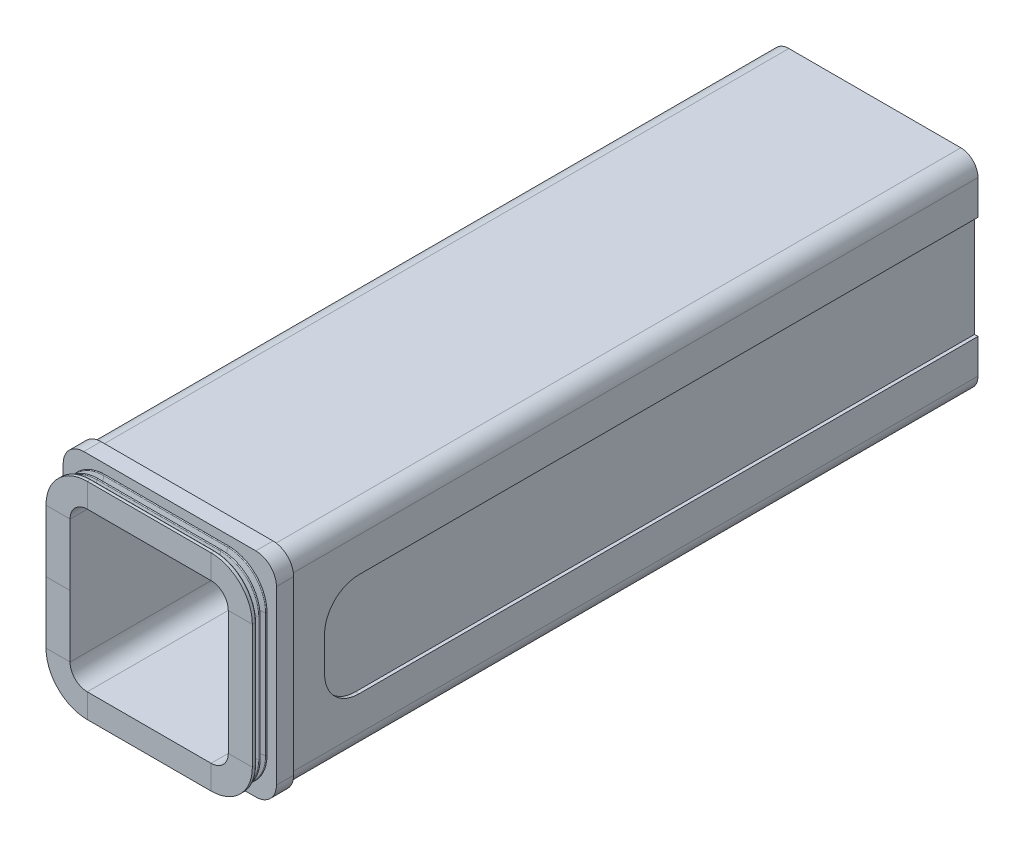
SolidWorks part; units mm, degrees
ref_plane "Front Plane" through (0, 0, 0) normal (0, 0, 1) x (1, 0, 0)
ref_plane "Top Plane" through (0, 0, 0) normal (0, 1, 0) x (1, 0, 0)
ref_plane "Right Plane" through (0, 0, 0) normal (1, 0, 0) x (0, 0, -1)
sketch "Sketch1" plane through (0, 0, 0) normal (0, 0, 1) x (1, 0, 0)
  line L1 (-25, -30) -> (25, -30)
  line L2 (-30, -25) -> (-30, 25)
  line L3 (-25, 30) -> (25, 30)
  line L4 (30, -25) -> (30, 25)
  line L5 (-30, -30) -> (30, 30) construction
  line L6 (-30, 30) -> (30, -30) construction
  arc A0 (-25, -30) -> (-30, -25) centre (-25, -25) cw
  arc A1 (25, -30) -> (30, -25) centre (25, -25) ccw
  arc A2 (25, 30) -> (30, 25) centre (25, 25) cw
  arc A3 (-30, 25) -> (-25, 30) centre (-25, 25) cw
  point P0 (0, 0)
  dimension "D3" = 5
  dimension "D1" = 60
  dimension "D2" = 60
extrude "Boss-Extrude1" add sketch "Sketch1" along normal blind 200
sketch "Sketch2" plane through (0, 0, 200) normal (0, 0, 1) x (1, 0, 0)
  line L8 (-25, -31) -> (25, -31)
  line L9 (31, -25) -> (31, 25)
  line L10 (25, 31) -> (-25, 31)
  line L11 (-31, 25) -> (-31, -25)
  line L12 (-25, -31) -> (25, -31)
  line L13 (31, -25) -> (31, 25)
  line L14 (25, 31) -> (-25, 31)
  line L15 (-31, 25) -> (-31, -25)
  arc A8 (-31, -25) -> (-25, -31) centre (-25, -25) ccw
  arc A9 (25, -31) -> (31, -25) centre (25, -25) ccw
  arc A10 (31, 25) -> (25, 31) centre (25, 25) ccw
  arc A11 (-25, 31) -> (-31, 25) centre (-25, 25) ccw
  arc A12 (-31, -25) -> (-25, -31) centre (-25, -25) ccw
  arc A13 (25, -31) -> (31, -25) centre (25, -25) ccw
  arc A14 (31, 25) -> (25, 31) centre (25, 25) ccw
  arc A15 (-25, 31) -> (-31, 25) centre (-25, 25) ccw
  dimension "D1" = 1
extrude "Boss-Extrude2" add sketch "Sketch2" along normal blind 5
ref_plane "Plane1" through (0, 0, 0) normal (0, 1, 0) x (1, 0, 0)
sketch "Sketch3" plane through (0, 0, 0) normal (0, 1, 0) x (1, 0, 0)
  line L0 (25, -205) -> (-25, -205) construction
  line L1 (25, -205) -> (-25, -205) construction
  line L2 (-25, -205) -> (-29.0194, -205.8039)
  line L3 (-29.0194, -206.1961) -> (-25.9806, -206.8039)
  line L4 (-25.9806, -207.1961) -> (-29.0194, -207.8039)
  line L5 (-29.0194, -208.1961) -> (-25.9806, -208.8039)
  line L6 (-25.9806, -209.1961) -> (-29.8392, -209.9678)
  line L7 (-30, -210.164) -> (-30, -211)
  line L8 (-30, -211) -> (-23, -211)
  line L9 (-23, -211) -> (-23, -205)
  line L10 (-23, -205) -> (-25, -205)
  line L11 (-30, -210) -> (-30, -208) construction
  line L12 (-30, -206) -> (-30, -208) construction
  line L13 (-30, -206) -> (-30, -205) construction
  line L14 (-30, -205) -> (-25, -205) construction
  arc A0 (-29.8392, -209.9678) -> (-30, -210.164) centre (-29.8, -210.164) ccw
  arc A1 (-29.0194, -205.8039) -> (-29.0194, -206.1961) centre (-28.9802, -206) ccw
  arc A2 (-29.0194, -207.8039) -> (-29.0194, -208.1961) centre (-28.9802, -208) ccw
  arc A3 (-25.9806, -208.8039) -> (-25.9806, -209.1961) centre (-26.0198, -209) cw
  arc A4 (-25.9806, -206.8039) -> (-25.9806, -207.1961) centre (-26.0198, -207) cw
  point P2 (0, 0)
  point P25 (-25, -207)
  dimension "D7" = 0.2
  dimension "D1" = 1
  dimension "D2" = 2
  dimension "D3" = 1
  dimension "D4" = 5
  dimension "D5" = 2
  dimension "D6" = 2
sketch "Sketch5" plane through (0, 0, 205) normal (0, 0, 1) x (1, 0, 0)
  line L1 (18, -23) -> (-18, -23)
  line L2 (23, -18) -> (23, 18)
  line L3 (18, 23) -> (-18, 23)
  line L4 (-23, -18) -> (-23, 18)
  line L5 (23, -23) -> (-23, 23) construction
  line L6 (23, 23) -> (-23, -23) construction
  arc A0 (-18, -23) -> (-23, -18) centre (-18, -18) cw
  arc A1 (18, -23) -> (23, -18) centre (18, -18) ccw
  arc A2 (23, 18) -> (18, 23) centre (18, 18) ccw
  arc A3 (-18, 23) -> (-23, 18) centre (-18, 18) ccw
  point P0 (0, 0)
  dimension "D1" = 5
sweep "Sweep1" add profiles "Sketch3" path "Sketch5"
sketch "Sketch6" plane through (0, 0, 205) normal (0, 0, 1) x (1, 0, 0)
  line L5 (-23, 18) -> (-23, 0)
  line L6 (-23, 0) -> (-23, -18)
  line L7 (-18, -23) -> (18, -23)
  line L8 (23, -18) -> (23, 18)
  line L9 (18, 23) -> (-18, 23)
  line L10 (-23, 18) -> (-23, 0)
  line L11 (-23, 0) -> (-23, -18)
  line L12 (-18, -23) -> (18, -23)
  line L13 (23, -18) -> (23, 18)
  line L14 (18, 23) -> (-18, 23)
  arc A4 (-23, -18) -> (-18, -23) centre (-18, -18) ccw
  arc A5 (18, -23) -> (23, -18) centre (18, -18) ccw
  arc A6 (23, 18) -> (18, 23) centre (18, 18) ccw
  arc A7 (-18, 23) -> (-23, 18) centre (-18, 18) ccw
  arc A8 (-23, -18) -> (-18, -23) centre (-18, -18) ccw
  arc A9 (18, -23) -> (23, -18) centre (18, -18) ccw
  arc A10 (23, 18) -> (18, 23) centre (18, 18) ccw
  arc A11 (-18, 23) -> (-23, 18) centre (-18, 18) ccw
  dimension "D1" = 0
extrude "Cut-Extrude1" cut sketch "Sketch6" against normal through all
sketch "Sketch7" plane through (-30, 0, 0) normal (-1, 0, 0) x (0, 0, 1)
  line L6 (0, 15) -> (0, -15)
  line L9 (0, -15) -> (190, -15)
  line L10 (190, -15) -> (190, 15)
  line L11 (190, 15) -> (0, 15)
  line L12 (0, -15) -> (190, -15)
  line L13 (190, -15) -> (190, 15)
  line L14 (190, 15) -> (0, 15)
  dimension "D1" = 10
extrude "Cut-Extrude2" cut sketch "Sketch7" against normal blind 1
fillet "Fillet1" radius 10 2 edges at (-29.5, -15, 190) (-29.5, 15, 190)
ref_plane "Plane2" through (0, 0, 0) normal (-1, 0, 0) x (0, 0, 1)
mirror "Mirror1" about plane through (0, 0, 0) normal (-1, 0, 0) of "Fillet1", "Cut-Extrude2"
